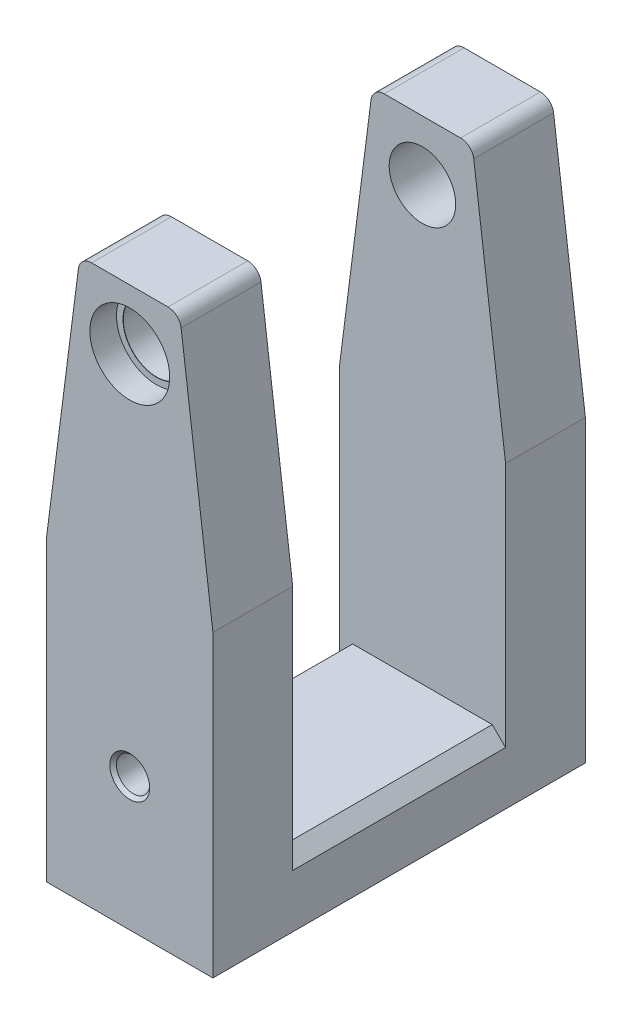
SolidWorks part; units mm, degrees
ref_plane "Front Plane" through (0, 0, 0) normal (0, 0, 1) x (1, 0, 0)
ref_plane "Top Plane" through (0, 0, 0) normal (0, 1, 0) x (1, 0, 0)
ref_plane "Right Plane" through (0, 0, 0) normal (1, 0, 0) x (0, 0, -1)
sketch "Sketch3" plane through (0, 0, 0) normal (0, 0, 1) x (1, 0, 0)
  line L0 (12.5, 0) -> (-12.5, 0)
  line L1 (-12.5, 0) -> (-12.5, 45)
  line L2 (-12.5, 45) -> (-7.5, 84)
  line L3 (-7.5, 84) -> (7.5, 84)
  line L4 (7.5, 84) -> (12.5, 45)
  line L5 (12.5, 45) -> (12.5, 0)
  line L6 (0, 0) -> (0, 84) construction
  dimension "D1" = 25
  dimension "D2" = 15
  dimension "D3" = 84
  dimension "D4" = 45
extrude "Boss-Extrude3" add sketch "Sketch3" along normal mid plane 56
sketch "Sketch4" plane through (12.5, 0, 0) normal (1, 0, 0) x (0, 0, -1)
  line L0 (-28, 84) -> (28, 84) construction
  line L1 (-16, 84) -> (16, 84)
  line L2 (-16, 84) -> (-16, 10)
  line L3 (-16, 10) -> (16, 10)
  line L4 (16, 84) -> (16, 10)
  line L5 (28, 45) -> (28, 84) construction
  line L6 (-28, 0) -> (28, 0) construction
  dimension "D1" = 12
  dimension "D2" = 32
  dimension "D3" = 10
extrude "Cut-Extrude2" cut sketch "Sketch4" against normal through all
hole_wizard "CBORE for M4 Hex Socket Head Cap Screw1" positions "Sketch5" profile "Sketch7" counterbore size "M4" standard "ISO"
sketch "Sketch5" plane through (0, 0, 28) normal (0, 0, 1) x (1, 0, 0)
  line L0 (0, 84) -> (0, 75) construction
  line L1 (7.5, 84) -> (-7.5, 84) construction
  point P0 (0, 75)
  point P8 (0, 0)
  dimension "D1" = 9
sketch "Sketch7" plane through (0, 75, 28) normal (1, 0, 0) x (0, -1, 0)
  line L0 (0, 0) -> (0, 23.0043)
  line L1 (0, 23.0043) -> (5, 20)
  line L2 (5, 20) -> (5, 4.025)
  line L3 (5, 4.025) -> (5.025, 4)
  line L4 (5.025, 4) -> (6, 4)
  line L5 (6, 4) -> (6, 0)
  line L6 (6, 0) -> (0, 0)
  line L9 (-5, 4.025) -> (-5.025, 4) construction
  line L10 (0, 23.0043) -> (-5, 20) construction
  line L11 (0, -6.35) -> (0, 107.95) construction
  dimension "Hole Dia." = 10
  dimension "Hole Depth" = 20
  dimension "C'Bore Dia." = 12
  dimension "C'Bore Depth" = 4
  dimension "Mid C'Sink Dia." = 10.05
  dimension "Mid C'Sink Angle" = 90
  dimension "Drill Angle" = 118
mirror "Mirror1" about plane through (0, 0, 0) normal (0, 0, 1) of "CBORE for M4 Hex Socket Head Cap Screw1"
hole_wizard "M6 Tapped Hole1" positions "Sketch17" profile "Sketch11" tap size "M6" standard "ISO"
sketch "Sketch17" plane through (0, 0, 28) normal (0, 0, 1) x (1, 0, 0)
  line L0 (0, 20) -> (0, 0) construction
  point P0 (0, 20)
  dimension "D1" = 20
sketch "Sketch11" plane through (0, 20, 28) normal (1, 0, 0) x (0, -1, 0)
  line L0 (0, 0) -> (0, 28.5022)
  line L1 (0, 28.5022) -> (2.5, 27)
  line L2 (2.5, 27) -> (2.5, 0.5)
  line L3 (2.5, 0.5) -> (3, 0)
  line L5 (3, 0) -> (0, 0)
  line L6 (-2.5, 0.5) -> (-3, 0) construction
  line L10 (0, 28.5022) -> (-2.5, 27) construction
  line L11 (0, -6.35) -> (0, 107.95) construction
  dimension "Tap Drill Dia." = 5
  dimension "Tap Drill Depth" = 27
  dimension "Near C'Sink Dia." = 6
  dimension "Near C'Sink Angle" = 90
  dimension "Drill Angle" = 118
cosmetic thread "Hole Thread1" parameters "D1"=12, "D2"=6
chamfer "Chamfer1" distance 2 angle 45 2 edges at (-12.5, 10, 0) (12.5, 10, 0)
fillet "Fillet2" radius 2 4 edges at (7.5, 84, -22) (-7.5, 84, 22) (7.5, 84, 22) (-7.5, 84, -22)
